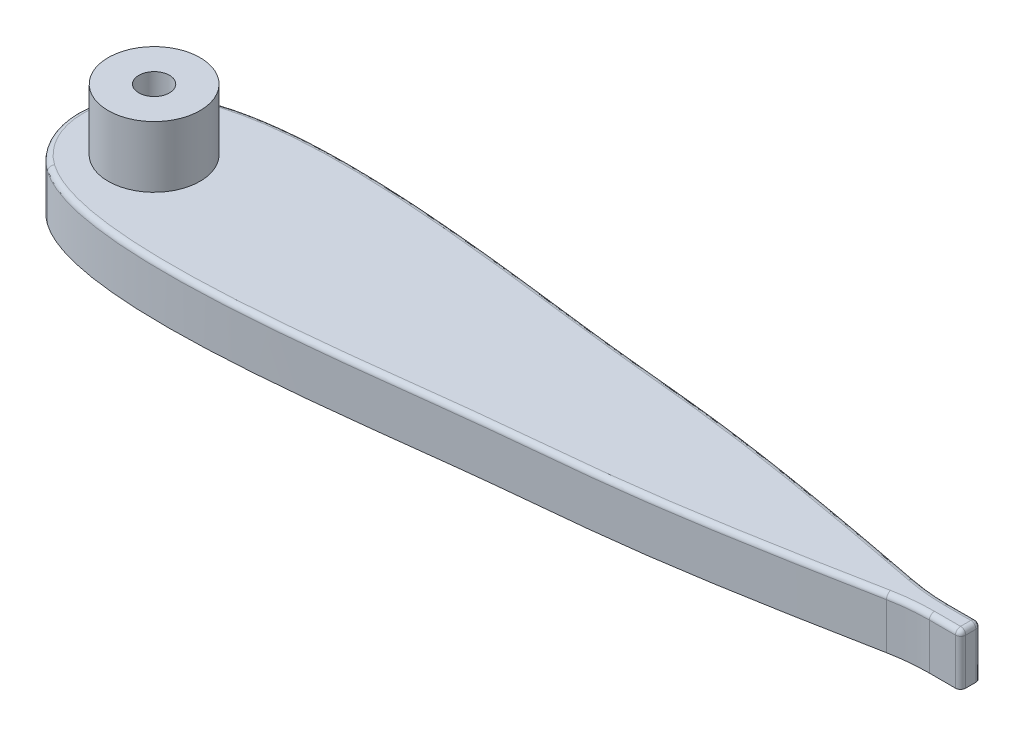
SolidWorks part; units mm, degrees
ref_plane "Ön Düzlem" through (0, 0, 0) normal (0, 0, 1) x (1, 0, 0)
ref_plane "Üst Düzlem" through (0, 0, 0) normal (0, 1, 0) x (1, 0, 0)
ref_plane "Sağ Düzlem" through (0, 0, 0) normal (1, 0, 0) x (0, 0, -1)
sketch "Sketch1" plane through (0, 0, 0) normal (0, 1, 0) x (1, 0, 0)
  line L0 (-55, 0) -> (55, 0) construction
  line L14 (75, 1) -> (80, 1)
  line L15 (75, 1) -> (75, -1)
  line L16 (75, -1) -> (80, -1)
  line L17 (80, 1) -> (80, -1)
  circle A0 centre (0, 0) radius 7.5
  spline S0 degree 3 poles (-4.3167, -6.1332) (3.1201, -11.3673) (46.4574, -4.6919) (51.3898, -5.7891) (80, 0) knots 0 0 0 0 0.498606 1 1 1 1
  spline S1 degree 3 poles (-4.3167, 6.1332) (3.1201, 11.3673) (46.4574, 4.6919) (51.3898, 5.7891) (80, 0) knots 0 0 0 0 0.498606 1 1 1 1
  point P10 (80, 0)
  dimension "D1" = 15
  dimension "D2" = 80
  dimension "D3" = 5
  dimension "D4" = 2
extrude "Boss-Extrude2" add sketch "Sketch1" along normal blind 5
fillet "Fillet1" radius 20 2 edges at (75, 2.5, -1) (75, 2.5, 1)
fillet "Fillet2" radius 0.5 2 edges at (80, 2.5, 1) (80, 2.5, -1)
fillet "Fillet3" radius 0.5 10 edges at (-7.5, 5, 0) (75.0201, 5, -1.0928) (78.2223, 5, -1) (79.8536, 5, -0.8536) (80, 5, 0) (79.8536, 5, 0.8536) (78.2223, 5, 1) (75.0201, 5, 1.0928)
sketch "Sketch3" plane through (0, 0, 0) normal (0, -1, 0) x (1, 0, 0)
  circle A0 centre (0, 0) radius 4.5
  dimension "D1" = 9
extrude "Boss-Extrude3" add sketch "Sketch3" against normal blind 6 from surface at -5 starting at face at (51.6668, 5, 0.1536)
sketch "Sketch4" plane through (0, 11, 0) normal (0, 1, 0) x (1, 0, 0)
  circle A0 centre (0, 0) radius 1.5
  dimension "D1" = 3
extrude "Cut-Extrude2" cut sketch "Sketch4" against normal blind 3
sketch "Sketch5" plane through (0, 0, 0) normal (0, -1, 0) x (1, 0, 0)
  circle A0 centre (0, 0) radius 1
  dimension "D1" = 2
extrude "Cut-Extrude3" cut sketch "Sketch5" against normal through all
sketch "Sketch6" plane through (0, 0, 0) normal (0, -1, 0) x (1, 0, 0)
  circle A0 centre (0, 0) radius 2.5
  dimension "D1" = 5
extrude "Cut-Extrude4" cut sketch "Sketch6" against normal offset from surface (6 mm away) 2 up to face at (0, 8, 1)
